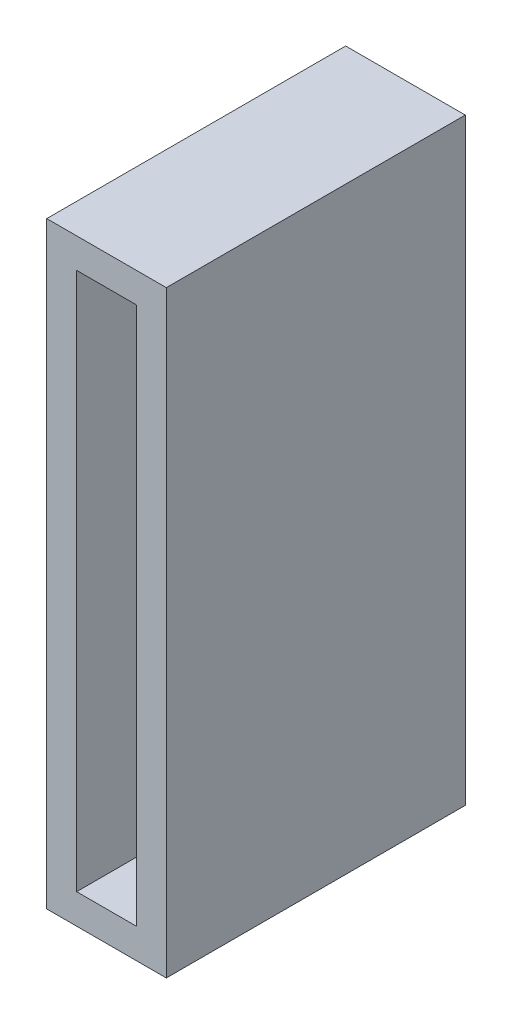
SolidWorks part; units mm, degrees
ref_plane "Plan de face" through (0, 0, 0) normal (0, 0, 1) x (1, 0, 0)
ref_plane "Plan de dessus" through (0, 0, 0) normal (0, 1, 0) x (1, 0, 0)
ref_plane "Plan de droite" through (0, 0, 0) normal (1, 0, 0) x (0, 0, -1)
sketch "Esquisse1" plane through (0, 0, 0) normal (0, 0, 1) x (1, 0, 0)
  line L0 (0, 200) -> (0, 0)
  line L1 (0, 200) -> (40, 200)
  line L2 (40, 200) -> (40, 0)
  line L3 (40, 0) -> (0, 0)
  line L4 (10, 190) -> (10, 10)
  line L5 (10, 10) -> (30, 10)
  line L6 (30, 10) -> (30, 190)
  line L7 (30, 190) -> (10, 190)
  dimension "D1" = 10
  dimension "D2" = 10
  dimension "D3" = 10
  dimension "D4" = 10
  dimension "D5" = 200
  dimension "D6" = 20
extrude "Boss.-Extru.2" add sketch "Esquisse1" along normal blind 100 contours L4 L5 L6 L7 | L0 L3 L2 L1
